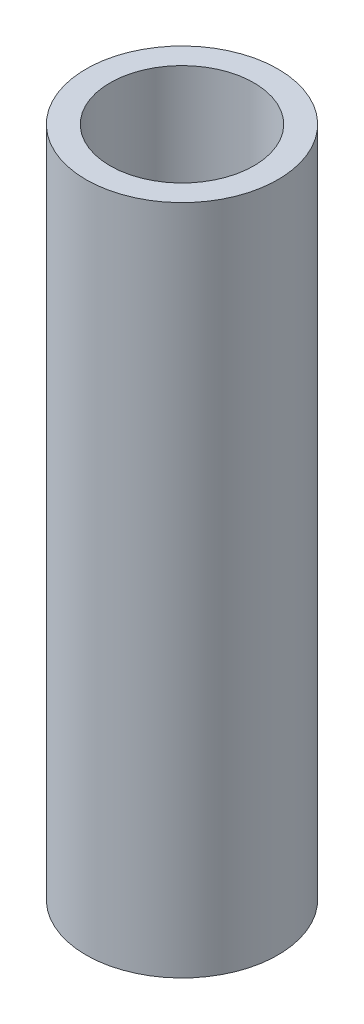
SolidWorks part; units mm, degrees
ref_plane "Front Plane" through (0, 0, 0) normal (0, 0, 1) x (1, 0, 0)
ref_plane "Top Plane" through (0, 0, 0) normal (0, 1, 0) x (1, 0, 0)
ref_plane "Right Plane" through (0, 0, 0) normal (1, 0, 0) x (0, 0, -1)
sketch "Sketch2" plane through (0, 0, 0) normal (0, 1, 0) x (1, 0, 0)
  circle A0 centre (-14.5676, 0) radius 12.7
  circle A2 centre (-14.5676, 0) radius 9.525
extrude "Boss-Extrude1" add sketch "Sketch2" along normal blind 88.9
